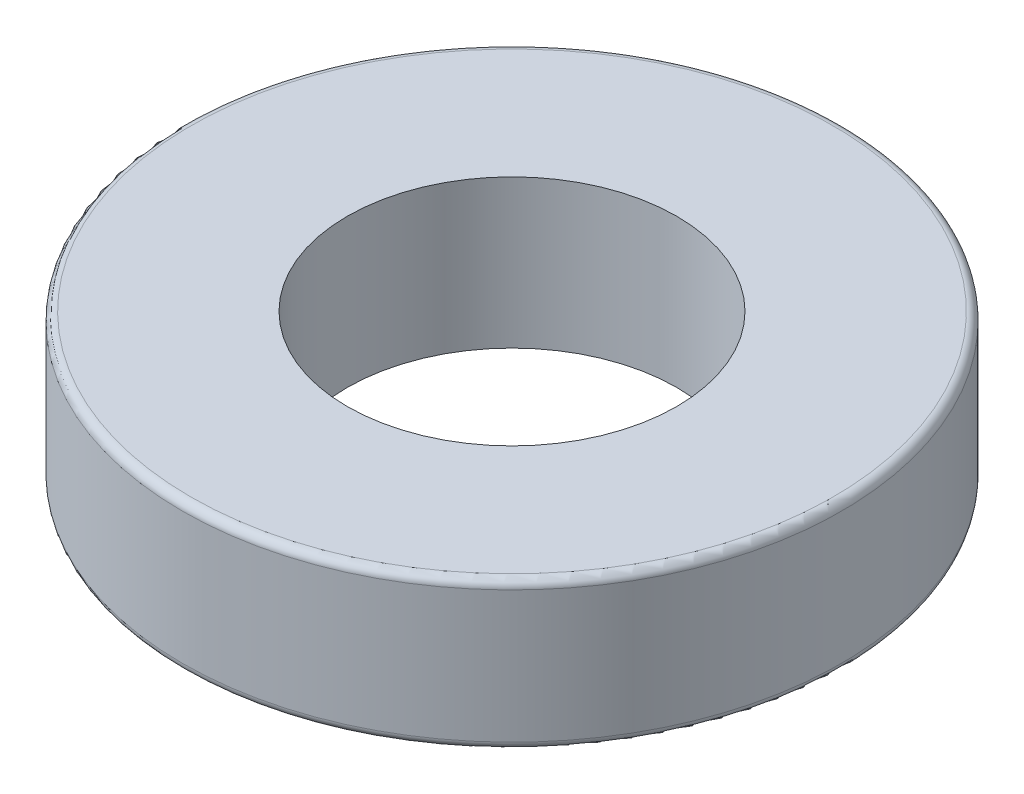
SolidWorks part; units mm, degrees
ref_plane "Front Plane" through (0, 0, 0) normal (0, 0, 1) x (1, 0, 0)
ref_plane "Top Plane" through (0, 0, 0) normal (0, 1, 0) x (1, 0, 0)
ref_plane "Right Plane" through (0, 0, 0) normal (1, 0, 0) x (0, 0, -1)
sketch "Sketch1" plane through (0, 0, 0) normal (0, 1, 0) x (1, 0, 0)
  circle A0 centre (0, 0) radius 20
  circle A1 centre (0, 0) radius 40
  dimension "D1" = 80
  dimension "D2" = 40
extrude "Boss-Extrude1" add sketch "Sketch1" along normal blind 18
fillet "Fillet1" radius 1 2 edges at (0, 0, 40) (0, 18, 40)
